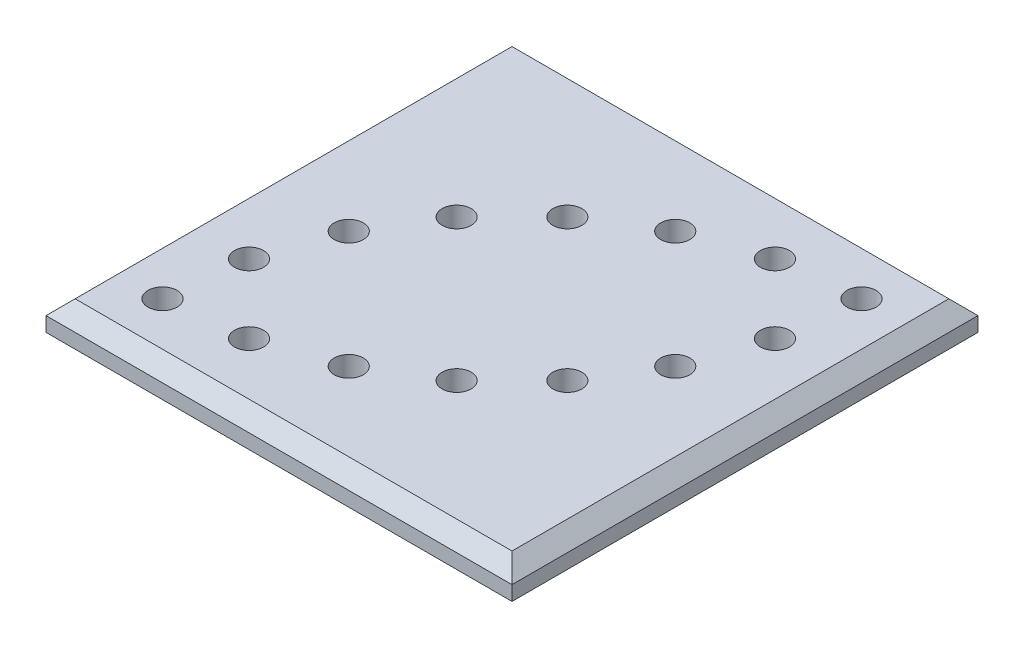
SolidWorks part; units mm, degrees
material "Al - 6061 Polished"
ref_plane "Front Plane" through (0, 0, 0) normal (0, 0, 1) x (1, 0, 0)
ref_plane "Top Plane" through (0, 0, 0) normal (0, 1, 0) x (1, 0, 0)
ref_plane "Right Plane" through (0, 0, 0) normal (1, 0, 0) x (0, 0, -1)
sketch "Sketch1" plane through (0, 0, 0) normal (0, 1, 0) x (1, 0, 0)
  line L2 (-50.8, -50.8) -> (50.8, -50.8)
  line L3 (-50.8, -50.8) -> (-50.8, 50.8)
  line L4 (-50.8, 50.8) -> (50.8, 50.8)
  line L5 (50.8, -50.8) -> (50.8, 50.8)
  line L6 (-50.8, -50.8) -> (50.8, 50.8) construction
  line L7 (-50.8, 50.8) -> (50.8, -50.8) construction
  point P2 (0, 0)
  dimension "D1" = 101.6
extrude "Boss-Extrude1" add sketch "Sketch1" along normal blind 9.525
sketch "Sketch2" plane through (0, 0, 0) normal (0, -1, 0) x (1, 0, 0)
  line L0 (47.498, 47.498) -> (-47.498, 47.498)
  line L1 (-47.498, 47.498) -> (-47.498, -47.498)
  line L2 (-47.498, -47.498) -> (47.498, -47.498)
  line L3 (47.498, -47.498) -> (47.498, 47.498)
  line L4 (50.8, -50.8) -> (50.8, 50.8)
  line L5 (50.8, 50.8) -> (-50.8, 50.8)
  line L6 (-50.8, 50.8) -> (-50.8, -50.8)
  line L7 (-50.8, -50.8) -> (50.8, -50.8)
  line L8 (50.8, -50.8) -> (50.8, 50.8)
  line L9 (50.8, 50.8) -> (-50.8, 50.8)
  line L10 (-50.8, 50.8) -> (-50.8, -50.8)
  line L11 (-50.8, -50.8) -> (50.8, -50.8)
  dimension "D1" = 0
  dimension "D2" = 3.302
extrude "Cut-Extrude1" cut sketch "Sketch2" against normal blind 3.175
chamfer "Chamfer1" distance 3.175 angle 45 4 edges at (0, 9.525, 50.8) (-50.8, 9.525, 0) (0, 9.525, -50.8) (50.8, 9.525, 0)
sketch "Sketch3" plane through (0, 9.525, 0) normal (0, 1, 0) x (1, 0, 0)
  line L0 (50.8, 50.8) -> (38.1, -38.1) construction
  line L1 (38.1, -38.1) -> (50.8, 50.8) construction
  line L2 (50.8, 50.8) -> (-38.1, 38.1) construction
  line L3 (38.1, 38.1) -> (38.1, -38.1) construction
  line L4 (38.1, 38.1) -> (38.1, -38.1) construction
  line L5 (38.1, -38.1) -> (114.3, -38.1) construction
  line L6 (38.1, -38.1) -> (38.1, 38.1) construction
  line L7 (38.1, -38.1) -> (21.1439, 36.1895) construction
  line L8 (-38.1, 38.1) -> (-38.1, -38.1) construction
  line L9 (-38.1, 38.1) -> (-21.1439, -36.1895) construction
  circle A0 centre (38.1, -38.1) radius 76.2 construction
  circle A3 centre (38.1, 38.1) radius 3.175 construction
  circle A4 centre (-38.1, 38.1) radius 76.2 construction
  circle A5 centre (21.1439, 36.1895) radius 3.175
  circle A6 centre (5.0381, 30.5538) radius 3.175
  circle A7 centre (-9.4099, 21.4756) radius 3.175
  circle A8 centre (-21.4756, 9.4099) radius 3.175
  circle A9 centre (-30.5538, -5.0381) radius 3.175
  circle A10 centre (-36.1895, -21.1439) radius 3.175
  circle A11 centre (-38.1, -38.1) radius 3.175
  circle A12 centre (-21.1439, -36.1895) radius 3.175
  circle A13 centre (-5.0381, -30.5538) radius 3.175
  circle A14 centre (9.4099, -21.4756) radius 3.175
  circle A15 centre (21.4756, -9.4099) radius 3.175
  circle A16 centre (30.5538, 5.0381) radius 3.175
  circle A17 centre (36.1895, 21.1439) radius 3.175
  circle A18 centre (38.1, 38.1) radius 3.175
  dimension "D5" = 152.4
  dimension "D6" = 6.35
  dimension "D1" = 88.9
  dimension "D2" = 12.7
  dimension "D3" = 88.9
  dimension "D4" = 12.7
  dimension "D7" = 90
  dimension "D9" = 12.857
  dimension "D11" = 12.857
  dimension "D8" = 8
  dimension "D10" = 8
extrude "Diana Hole Pattern" cut sketch "Sketch3" against normal through all
sketch "Sketch9" [suppressed] plane through (0, 0, 0) normal (0, 1, 0) x (1, 0, 0)
  circle A0 centre (0, 0) radius 3.175
  circle A11 centre (19.05, 0) radius 3.175
  circle A12 centre (0, -19.05) radius 3.175
  circle A13 centre (-19.05, 0) radius 3.175
  circle A14 centre (0, 19.05) radius 3.175
  circle A16 centre (38.1, 0) radius 3.175
  circle A17 centre (26.9408, -26.9408) radius 3.175
  circle A18 centre (0, -38.1) radius 3.175
  circle A19 centre (-26.9408, -26.9408) radius 3.175
  circle A20 centre (-38.1, 0) radius 3.175
  circle A21 centre (-26.9408, 26.9408) radius 3.175
  circle A22 centre (0, 38.1) radius 3.175
  circle A23 centre (26.9408, 26.9408) radius 3.175
  point P14 (0, 0)
  point P15 (0, 0)
  dimension "D1" = 6.35
  dimension "D3" = 4
  dimension "D2" = 19.05
  dimension "D4" = 38.1
  dimension "D5" = 8
sketch "Sketch10" [suppressed] plane through (0, 0, 0) normal (0, -1, 0) x (1, 0, 0)
extrude "Cut-Extrude3" [suppressed] cut sketch "Sketch9" along normal blind 55.118
sketch "Sketch11" [suppressed] plane through (0, 9.525, 0) normal (0, 1, 0) x (1, 0, 0)
  circle A0 centre (0, 0) radius 3.175
  dimension "D1" = 6.35
